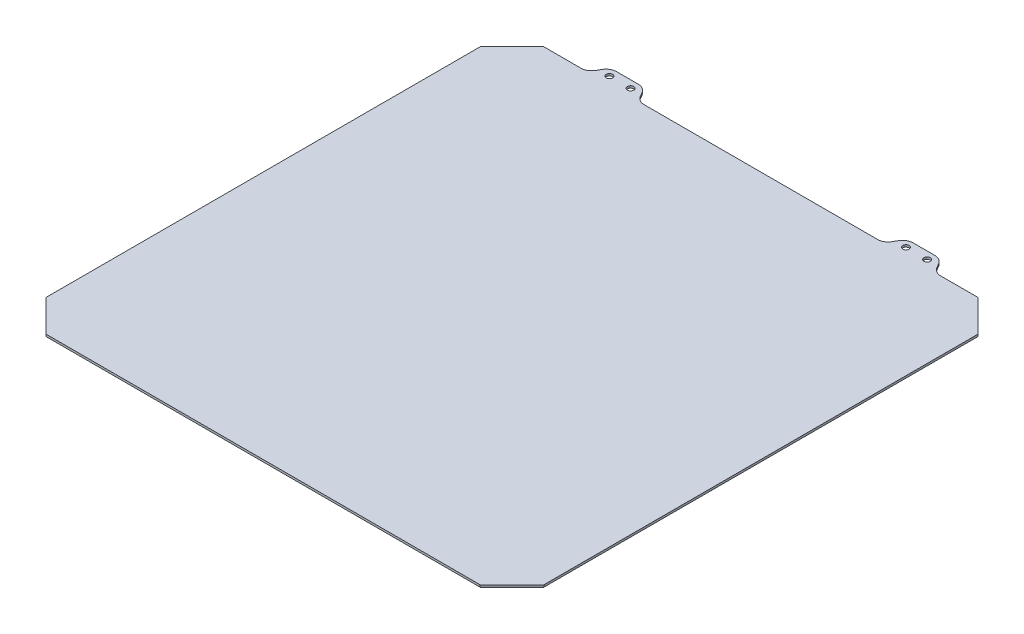
SolidWorks part; units mm, degrees
ref_plane "Front" through (0, 0, 0) normal (0, 0, 1) x (1, 0, 0)
ref_plane "Top" through (0, 0, 0) normal (0, 1, 0) x (1, 0, 0)
ref_plane "Right" through (0, 0, 0) normal (1, 0, 0) x (0, 0, -1)
sketch "Sketch1" plane through (0, 0, 0) normal (0, 1, 0) x (1, 0, 0)
  line L1 (117.5, 117.5) -> (-117.5, 117.5)
  line L2 (117.5, 117.5) -> (117.5, -117.5)
  line L3 (117.5, -117.5) -> (-117.5, -117.5)
  line L4 (-117.5, 117.5) -> (-117.5, -117.5)
  line L5 (0, -117.5) -> (0, 117.5) construction
  line L6 (117.5, 0) -> (-117.5, 0) construction
  point P0 (0, 0)
  dimension "D1" = 235
extrude "Boss-Extrude1" add sketch "Sketch1" along normal blind 1
sketch "Sketch2" plane through (0, 0, 0) normal (0, 1, 0) x (1, 0, 0)
  line L0 (-82.0415, 117.5) -> (-78, 124.5)
  line L1 (117.5, 117.5) -> (-117.5, 117.5) construction
  line L2 (-78, 124.5) -> (-62, 124.5)
  line L3 (-62, 124.5) -> (-57.9585, 117.5)
  line L4 (-57.9585, 117.5) -> (-82.0415, 117.5)
  line L5 (-70, 124.5) -> (-70, 117.5) construction
  line L6 (-75, 121) -> (-65, 121) construction
  line L7 (0, 0) -> (0, 117.5) construction
  line L8 (57.9585, 117.5) -> (82.0415, 117.5)
  line L9 (62, 124.5) -> (57.9585, 117.5)
  line L10 (75, 121) -> (65, 121) construction
  line L11 (70, 124.5) -> (70, 117.5) construction
  line L12 (78, 124.5) -> (62, 124.5)
  line L13 (82.0415, 117.5) -> (78, 124.5)
  circle A0 centre (-75, 121) radius 1.5
  circle A1 centre (-65, 121) radius 1.5
  circle A2 centre (65, 121) radius 1.5
  circle A3 centre (75, 121) radius 1.5
  point P12 (-70, 121)
  dimension "D2" = 3
  dimension "D1" = 10
  dimension "D3" = 60
  dimension "D4" = 7
  dimension "D5" = 16
  dimension "D6" = 130
extrude "Boss-Extrude2" add sketch "Sketch2" along normal blind 1
fillet "Fillet1" radius 5 8 edges at (-78, 0.5, -124.5) (-62, 0.5, -124.5) (-57.9585, 0.5, -117.5) (57.9585, 0.5, -117.5) (62, 0.5, -124.5) (78, 0.5, -124.5) (82.0415, 0.5, -117.5) (-82.0415, 0.5, -117.5)
chamfer "Chamfer1" distance 15 angle 45 4 edges at (117.5, 0.5, -117.5) (117.5, 0.5, 117.5) (-117.5, 0.5, 117.5) (-117.5, 0.5, -117.5)
